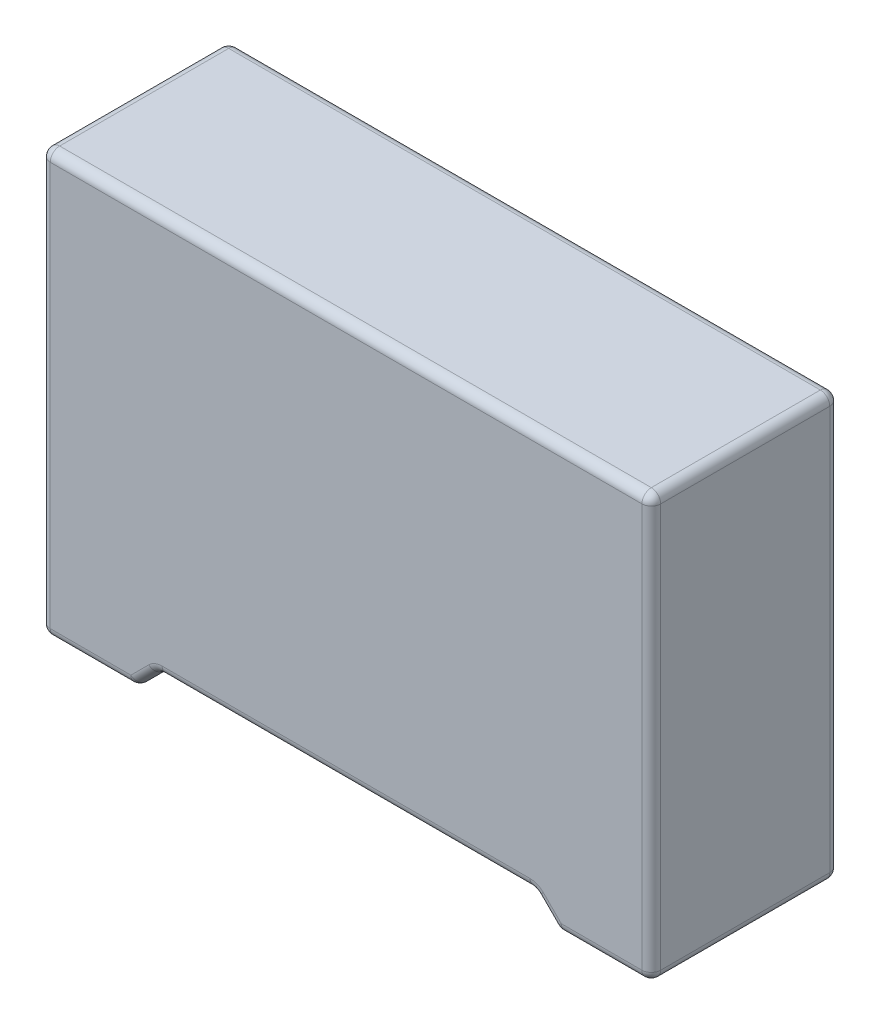
SolidWorks part; units mm, degrees
ref_plane "Front Plane" through (0, 0, 0) normal (0, 0, 1) x (1, 0, 0)
ref_plane "Top Plane" through (0, 0, 0) normal (0, 1, 0) x (1, 0, 0)
ref_plane "Right Plane" through (0, 0, 0) normal (1, 0, 0) x (0, 0, -1)
sketch "Sketch1" plane through (0, 0, 0) normal (0, 1, 0) x (1, 0, 0)
  line L0 (6.5, -2) -> (-6.5, 2) construction
  line L1 (-6.5, 2) -> (6.5, 2)
  line L2 (-6.5, 2) -> (-6.5, -2)
  line L3 (-6.5, -2) -> (6.5, -2)
  line L4 (6.5, 2) -> (6.5, -2)
  dimension "D1" = 13
  dimension "D2" = 4
extrude "Boss-Extrude1" add sketch "Sketch1" along normal blind 9
sketch "Sketch2" plane through (0, 0, 2) normal (0, 0, 1) x (1, 0, 0)
  line L0 (-4.5, 0) -> (-4, 0.5)
  line L1 (-6.5, 0) -> (6.5, 0) construction
  line L2 (-4, 0.5) -> (4, 0.5)
  line L3 (4, 0.5) -> (4.5, 0)
  line L4 (4.5, 0) -> (4.5, -1.5)
  line L5 (4.5, -1.5) -> (-4.5, -1.5)
  line L6 (-4.5, -1.5) -> (-4.5, 0)
  line L7 (0, 0) -> (0, 0.5) construction
  dimension "D1" = 2
  dimension "D2" = 0.5
  dimension "D3" = 45
  dimension "D4" = 2
extrude "Cut-Extrude1" cut sketch "Sketch2" against normal through all
sketch "Sketch3" plane through (0, 0, 0) normal (0, -1, 0) x (1, 0, 0)
  line L0 (-5, 0) -> (5, 0) construction
  circle A0 centre (5, 0) radius 0.3
  circle A1 centre (-5, 0) radius 0.3
  dimension "D1" = 0.6
  dimension "D2" = 10
extrude "Boss-Extrude2" add sketch "Sketch3" along normal blind 1
fillet "Fillet1" radius 0.2 24 edges at (6.5, 0, 0) (4.25, 0.25, -2) (5.5, 0, -2) (6.5, 4.5, -2) (-5.5, 0, -2) (-4.25, 0.25, -2) (0, 0.5, -2) (-6.5, 4.5, -2) (-6.5, 0, 0) (0, 9, -2) (6.5, 9, 0) (-6.5, 9, 0) (-6.5, 4.5, 2) (0, 9, 2) (6.5, 4.5, 2) (5.5, 0, 2) (4.25, 0.25, 2) (0, 0.5, 2) (-4.25, 0.25, 2) (-5.5, 0, 2) (4.5, 0, 0) (-4.5, 0, 0) (-4, 0.5, 0) (4, 0.5, 0)
